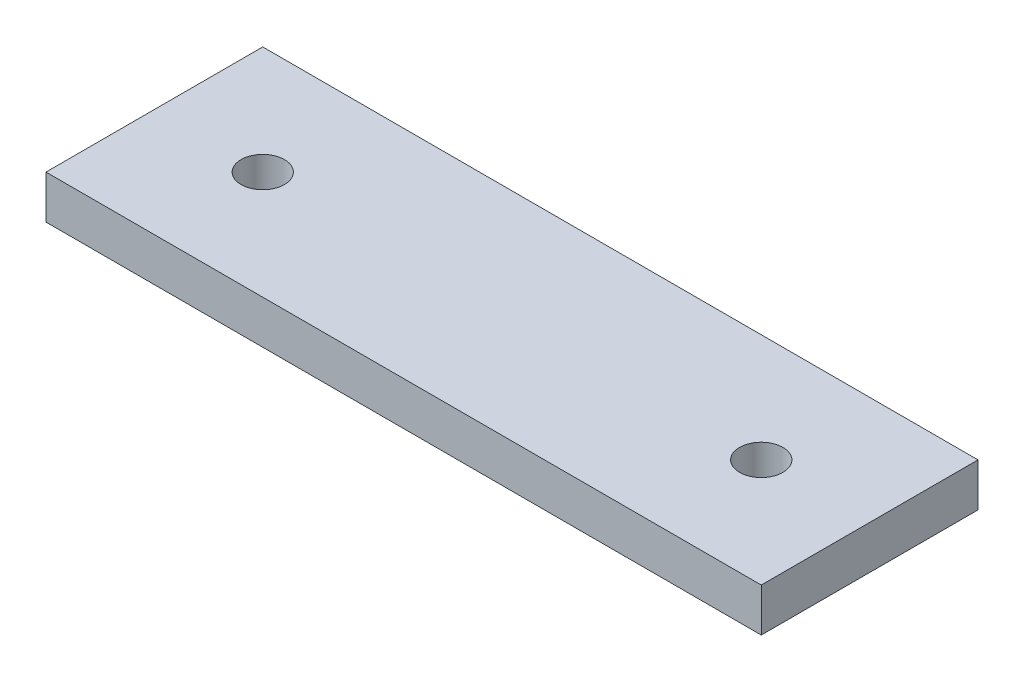
SolidWorks part; units mm, degrees
ref_plane "Front Plane" through (0, 0, 0) normal (0, 0, 1) x (1, 0, 0)
ref_plane "Top Plane" through (0, 0, 0) normal (0, 1, 0) x (1, 0, 0)
ref_plane "Right Plane" through (0, 0, 0) normal (1, 0, 0) x (0, 0, -1)
sketch "Sketch1" plane through (0, 0, 0) normal (0, 1, 0) x (1, 0, 0)
  line L1 (0, 0) -> (66, 0)
  line L2 (0, 0) -> (0, -20)
  line L3 (0, -20) -> (66, -20)
  line L4 (66, 0) -> (66, -20)
  dimension "D1" = 66
  dimension "D2" = 20
extrude "Boss-Extrude1" add sketch "Sketch1" along normal blind 4
sketch "Sketch2" plane through (0, 4, 0) normal (0, 1, 0) x (1, 0, 0)
  line L0 (0, -10) -> (66, -10) construction
  line L1 (0, 0) -> (0, -20) construction
  line L2 (66, -20) -> (66, 0) construction
  circle A0 centre (10, -10) radius 2
  circle A1 centre (56, -10) radius 2
  dimension "D1" = 4
  dimension "D2" = 10
  dimension "D3" = 10
extrude "Cut-Extrude1" cut sketch "Sketch2" against normal through all
equation "\"D3@Sketch2\"=\"D2@Sketch2\""
